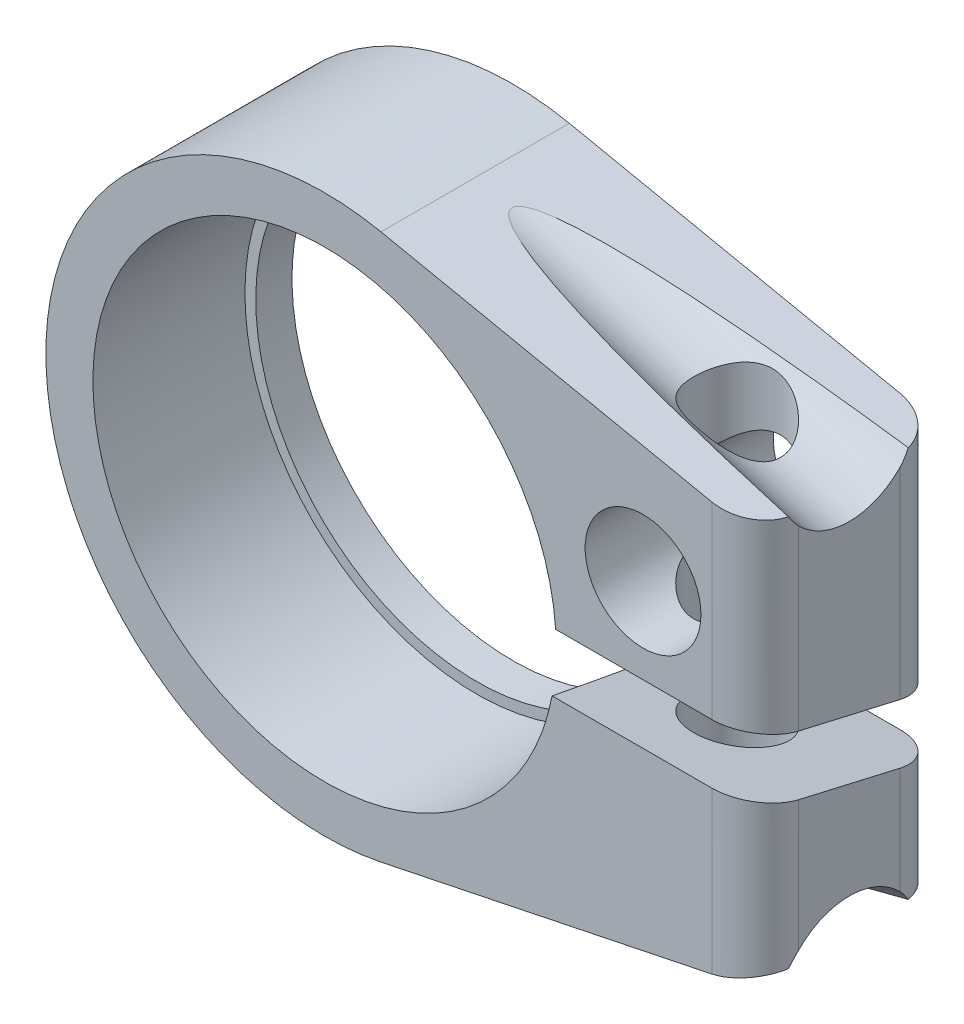
SolidWorks part; units mm, degrees
ref_plane "Plan de face" through (0, 0, 0) normal (0, 0, 1) x (1, 0, 0)
ref_plane "Plan de dessus" through (0, 0, 0) normal (0, 1, 0) x (1, 0, 0)
ref_plane "Plan de droite" through (0, 0, 0) normal (1, 0, 0) x (0, 0, -1)
sketch "Esquisse1" plane through (0, 0, 0) normal (0, 0, 1) x (1, 0, 0)
  line L0 (0, 0) -> (42.8373, 0) construction
  line L1 (3.9019, 18.8504) -> (29.75, 13.5)
  line L2 (3.9019, -18.8504) -> (29.75, -13.5)
  line L3 (29.75, 13.5) -> (29.75, -13.5)
  arc A0 (3.9019, 18.8504) -> (3.9019, -18.8504) centre (0, 0) ccw
  circle A1 centre (0, 0) radius 15.25
  dimension "D1" = 38.5
  dimension "D3" = 49
  dimension "D4" = 30.5
  dimension "D2" = 27
extrude "Extrusion1" add sketch "Esquisse1" along normal mid plane 13
sketch "Esquisse2" plane through (0, 0, 6.5) normal (0, 0, 1) x (1, 0, 0)
  circle A0 centre (0, 0) radius 16
  dimension "D1" = 32
extrude "Enlèv. mat.-Extru.1" cut sketch "Esquisse2" against normal blind 10.5
sketch "Esquisse3" plane through (29.75, 0, 0) normal (1, 0, 0) x (0, 0, -1)
  line L0 (6.5, -6) -> (-6.5, -2.9987)
  line L1 (6.5, -13.5) -> (6.5, 13.5) construction
  line L2 (-6.5, -13.5) -> (-6.5, 13.5) construction
  line L3 (-6.5, -2.9987) -> (-6.5, 1.1065)
  line L4 (-6.5, 1.1065) -> (6.5, -1.8948)
  line L5 (6.5, -1.8948) -> (6.5, -6)
  line L6 (0, 0) -> (-20.7853, 0) construction
  dimension "D1" = 4
  dimension "D2" = 7.5
  dimension "D3" = 13
extrude "Enlèv. mat.-Extru.2" cut sketch "Esquisse3" against normal up to next
sketch "Esquisse4" plane through (0, 0, 6.5) normal (0, 0, 1) x (1, 0, 0)
  circle A0 centre (22, 7) radius 4
  dimension "D1" = 8
  dimension "D2" = 22
  dimension "D3" = 7
extrude "Enlèv. mat.-Extru.3" cut sketch "Esquisse4" against normal through all
fillet "Congé2" radius 3 4 edges at (29.75, -8.2494, 6.5) (29.75, 5.8026, -6.5) (29.75, 7.3033, 6.5) (29.75, -9.75, -6.5)
sketch "Esquisse5" plane through (0, 0, 0) normal (0, 1, 0) x (1, 0, 0)
  line L0 (22, 6.5) -> (22, -6.5) construction
  circle A0 centre (22, 0) radius 3
  dimension "D1" = 6
extrude "Enlèv. mat.-Extru.4" cut sketch "Esquisse5" against normal through all and the other way through all
sketch "Esquisse6" plane through (0, 0, 0) normal (0, 1, 0) x (1, 0, 0)
  line L0 (22, 6.5) -> (22, -6.5) construction
  circle A0 centre (22, 0) radius 4.5
  circle A1 centre (22, 0) radius 3 construction
  dimension "D1" = 9
extrude "Enlèv. mat.-Extru.5" cut sketch "Esquisse6" against normal through all from offset 10
sketch "Esquisse7" plane through (0, 0, 0) normal (0, 0, 1) x (1, 0, 0)
  line L0 (0, 0) -> (32.1464, 0) construction
  line L1 (-29.6849, -34.5995) -> (62.3469, -6.4626) construction
  line L2 (7.9176, -23.1033) -> (6.4557, -18.3218)
  line L3 (6.4557, -18.3218) -> (29.75, -11.2)
  line L4 (29.75, -11.2) -> (31.2119, -15.9815)
  line L5 (31.2119, -15.9815) -> (7.9176, -23.1033)
  line L6 (29.75, -3.6913) -> (29.75, -13.5) construction
  line L7 (3.9019, -18.8504) -> (26.75, -14.121) construction
  dimension "D1" = 17
  dimension "D2" = 10
  dimension "D3" = 11.2
revolve "Enlèvement de matière-Révolution1" cut sketch "Esquisse7" angle 360 about L1
mirror "Symétrie1" about plane through (0, 0, 0) normal (0, 1, 0) of "Enlèvement de matière-Révolution1"
